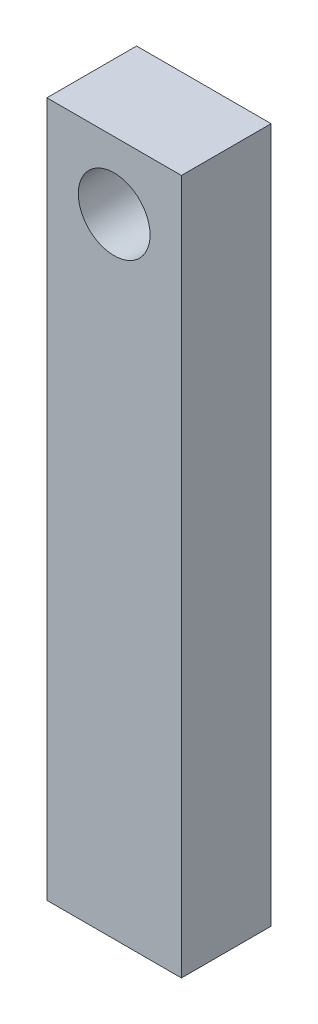
SolidWorks part; units mm, degrees
ref_plane "前基準面" through (0, 0, 0) normal (0, 0, 1) x (1, 0, 0)
ref_plane "上基準面" through (0, 0, 0) normal (0, 1, 0) x (1, 0, 0)
ref_plane "右基準面" through (0, 0, 0) normal (1, 0, 0) x (0, 0, -1)
sketch "草圖1" plane through (0, 0, 0) normal (0, 0, 1) x (1, 0, 0)
  line L1 (-7.5, -38.75) -> (7.5, -38.75)
  line L2 (-7.5, -38.75) -> (-7.5, 38.75)
  line L3 (-7.5, 38.75) -> (7.5, 38.75)
  line L4 (7.5, -38.75) -> (7.5, 38.75)
  line L5 (-7.5, -38.75) -> (7.5, 38.75) construction
  line L6 (-7.5, 38.75) -> (7.5, -38.75) construction
  circle A0 centre (0, 31.25) radius 4
  point P0 (0, 0)
  dimension "D3" = 70
  dimension "D4" = 8
  dimension "D1" = 77.5
  dimension "D2" = 15
extrude "填料-伸長1" add sketch "草圖1" along normal blind 10
